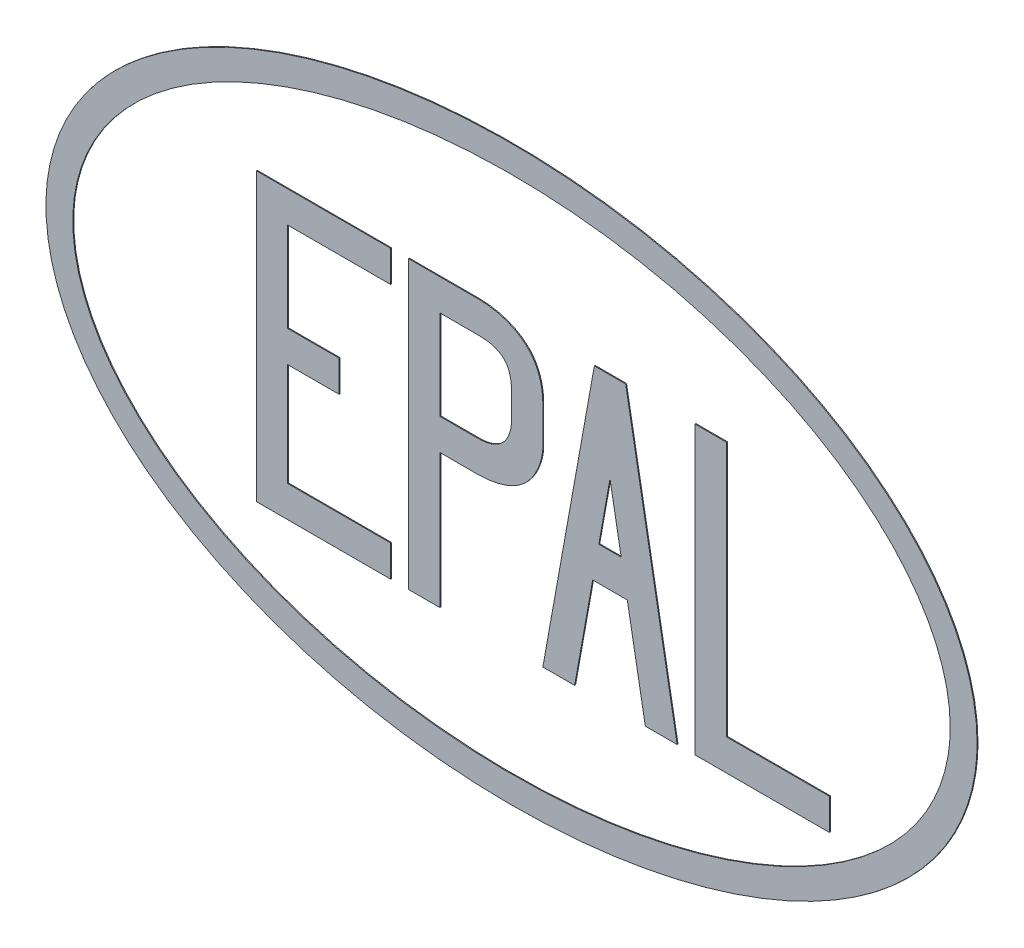
SolidWorks part; units mm, degrees
ref_plane "front" through (0, 0, 0) normal (0, 0, 1) x (1, 0, 0)
ref_plane "top" through (0, 0, 0) normal (0, 1, 0) x (1, 0, 0)
ref_plane "right" through (0, 0, 0) normal (1, 0, 0) x (0, 0, -1)
sketch "Sketch2" plane through (0, 0, 0) normal (0, 0, 1) x (1, 0, 0)
  line L2 (-28.5, -16.9) -> (-28.5, 15.1)
  line L3 (-28.5, 15.1) -> (-13.5, 15.1)
  line L4 (-13.5, 15.1) -> (-13.5, 11.6)
  line L5 (-13.5, 11.6) -> (-25, 11.6)
  line L6 (-25, 11.6) -> (-25, 1.6)
  line L7 (-25, 1.6) -> (-19.25, 1.6)
  line L8 (-19.25, 1.6) -> (-19.25, -1.9)
  line L9 (-19.25, -1.9) -> (-25, -1.9)
  line L10 (-25, -1.9) -> (-25, -13.4)
  line L11 (-25, -13.4) -> (-13.5, -13.4)
  line L12 (-13.5, -13.4) -> (-13.5, -16.9)
  line L13 (-13.5, -16.9) -> (-28.5, -16.9)
  line L14 (-28.5, -16.9) -> (-26.2062, -16.7418)
  line L15 (-11.5, 15.1) -> (-11.5, -16.9)
  line L16 (-11.5, -16.9) -> (-8, -16.9)
  line L17 (-8, -16.9) -> (-8, -1.9)
  line L18 (-8, -1.9) -> (-3.7272, -1.9)
  line L19 (-3.7272, 15.1) -> (-11.5, 15.1)
  line L20 (-3.7272, 11.6) -> (-8, 11.6)
  line L21 (-8, 11.6) -> (-8, 1.6)
  line L22 (-8, 1.6) -> (-3.7272, 1.6)
  line L23 (35.5, -16.9) -> (20.5, -16.9)
  line L24 (20.5, -16.9) -> (20.5, 15.1)
  line L25 (20.5, 15.1) -> (24, 15.1)
  line L26 (24, 15.1) -> (24, -13.4)
  line L27 (24, -13.4) -> (35.5, -13.4)
  line L28 (35.5, -13.4) -> (35.5, -16.9)
  line L29 (9.0689, -5.698) -> (7.0561, -16.9)
  line L30 (7.0561, -16.9) -> (3.5, -16.9)
  line L31 (3.5, -16.9) -> (9.25, 15.1)
  line L32 (9.25, 15.1) -> (12.75, 15.1)
  line L33 (12.75, 15.1) -> (18.5, -16.9)
  line L34 (18.5, -16.9) -> (14.9439, -16.9)
  line L35 (14.9439, -16.9) -> (12.9311, -5.698)
  line L36 (12.9311, -5.698) -> (9.0689, -5.698)
  line L37 (9.7514, -1.9) -> (11, 5.0489)
  line L38 (11, 5.0489) -> (12.2486, -1.9)
  line L39 (12.2486, -1.9) -> (9.7514, -1.9)
  line L40 (0, 8.0603) -> (0, 5.1397)
  line L41 (3.5, 8.5766) -> (3.5, 4.4026)
  line L42 (-1023.098, -13.4) -> (48976.902, -13.4) construction
  line L43 (-1016.6827, -1.9) -> (48983.3173, -1.9) construction
  line L44 (-1013.475, 1.6) -> (48986.525, 1.6) construction
  line L45 (-1019.5495, 11.6) -> (48980.4505, 11.6) construction
  line L46 (-1024.1004, 15.1) -> (48975.8996, 15.1) construction
  line L48 (-1024.7018, -16.9) -> (48975.2982, -16.9) construction
  spline S0 degree 3 poles (-3.7272, 15.1) (-1.172, 15.1) (2.8563, 13.4046) (3.5, 9.8113) (3.5, 8.5766) knots 0 0 0 0 0.562071 1 1 1 1
  spline S1 degree 3 poles (-3.7272, 11.6) (-1.0902, 11.6) (0, 10.5384) (0, 8.0603) knots 0 0 0 0 1 1 1 1
  spline S2 degree 3 poles (46.4484, -11.387) (50.2758, 0) (46.4484, 11.387) (35.5506, 21.0397) (19.24, 27.49) (0, 29.755) (-19.24, 27.49) (-35.5506, 21.0397) (-46.4484, 11.387) (-50.2758, 0) (-46.4484, -11.387) (-35.5506, -21.0397) (-19.24, -27.49) (0, -29.755) (19.24, -27.49) (35.5506, -21.0397) (46.4484, -11.387) (50.2758, 0) (46.4484, 11.387) knots -1.178097 -0.785398 -0.392699 0 0.392699 0.785398 1.178097 1.570796 1.963495 2.356194 2.748894 3.141593 3.534292 3.926991 4.31969 4.712389 5.105088 5.497787 5.890486 6.283185 6.675884 7.068583 7.461283 only from (49, 0) to (49, 0)
  spline S3 degree 3 poles (-3.7272, 1.6) (-0.4277, 1.6) (0, 4.185) (0, 5.1397) knots 0 0 0 0 1 1 1 1
  spline S4 degree 3 poles (51.252, -6.6868) (52.374, 0) (51.252, 6.6868) (46.9571, 15.0148) (37.0451, 23.7028) (19.9374, 30.4384) (0, 32.7808) (-19.9374, 30.4384) (-37.0451, 23.7028) (-46.9571, 15.0148) (-51.252, 6.6868) (-52.374, 0) (-51.252, -6.6868) (-46.9571, -15.0148) (-37.0451, -23.7028) (-19.9374, -30.4384) (0, -32.7808) (19.9374, -30.4384) (37.0451, -23.7028) (46.9571, -15.0148) (51.252, -6.6868) (52.374, 0) (51.252, 6.6868) knots -0.785398 -0.392699 -0.19635 0 0.19635 0.392699 0.785398 1.178097 1.570796 1.963495 2.356194 2.748894 2.945243 3.141593 3.337942 3.534292 3.926991 4.31969 4.712389 5.105088 5.497787 5.890486 6.086836 6.283185 6.479535 6.675884 7.068583 only from (52, 0) to (52, 0)
  spline S5 degree 3 poles (-3.7272, -1.9) (-1.8006, -1.9) (2.0924, -0.8987) (3.5, 3.1462) (3.5, 4.4026) knots 0 0 0 0 0.575012 1 1 1 1
  point P58 (-19.25, 11.6)
  point P62 (-19.25, -13.4)
  point P66 (11, 15.1)
  dimension "D1" = 32
  dimension "D2" = 3.5
  dimension "D3" = 3.5
  dimension "D4" = 3.5
  dimension "D5" = 15
  dimension "D6" = 3.5
  dimension "D7" = 2
  dimension "D8" = 2
  dimension "D9" = 3.5
  dimension "D10" = 3.5
  dimension "D11" = 3.5
  dimension "D12" = 3.5
  dimension "D13" = 15
  dimension "D14" = 15
  dimension "D15" = 15
  dimension "D16" = 15
  dimension "D17" = 3.5
  dimension "D18" = 9.5
  dimension "D19" = 3.5
  dimension "D20" = 1.6
extrude "Boss-Extrude2" add sketch "Sketch2" along normal blind 0.1 contours S4 | S2 | L2 L3 L4 L5 L6 L7 L8 L9 L10 L11 L12 L13 | L15 L16 L17 L18 S5 L41 S0 L19 | L21 L22 S3 L40 S1 L20 | L31 L32 L33 L34 L35 L36 L29 L30 | L37 L38 L39 | L24 L25 L26 L27 L28 L23
